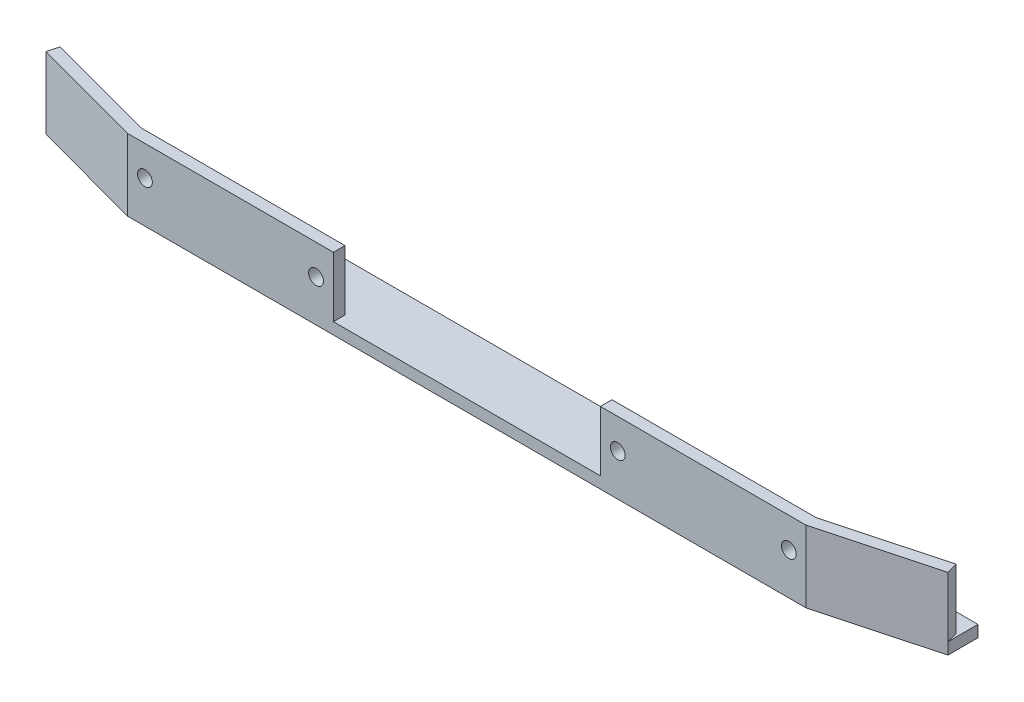
SolidWorks part; units mm, degrees
ref_plane "Front Plane" through (0, 0, 0) normal (0, 0, 1) x (1, 0, 0)
ref_plane "Top Plane" through (0, 0, 0) normal (0, 1, 0) x (1, 0, 0)
ref_plane "Right Plane" through (0, 0, 0) normal (1, 0, 0) x (0, 0, -1)
sketch "Sketch1" plane through (0, 0, 0) normal (0, 1, 0) x (1, 0, 0)
  line L0 (-58.6068, 6.5) -> (-34.4666, 0)
  line L1 (-58.6068, 13) -> (136.3932, 13)
  line L2 (-58.6068, 13) -> (-58.6068, 6.5)
  line L3 (-34.4666, 0) -> (112.253, 0)
  line L4 (136.3932, 13) -> (136.3932, 6.5)
  line L5 (136.3932, 6.5) -> (112.253, 0)
  circle A0 centre (-11.6068, 9.25) radius 1.5
  circle A1 centre (89.3932, 9.25) radius 1.5
  point P12 (0, 0)
  dimension "D7" = 9.25
  dimension "D8" = 3
  dimension "D2" = 195
  dimension "D3" = 25
  dimension "D4" = 25
  dimension "D5" = 13
  dimension "D10" = 2
extrude "Boss-Extrude1" add sketch "Sketch1" along normal blind 2.5
sketch "Sketch2" plane through (0, 2.5, 0) normal (0, 1, 0) x (1, 0, 0)
  line L0 (-58.6068, 6.5) -> (-34.4666, 0)
  line L1 (-34.4666, 0) -> (10.0334, 0)
  line L2 (-34.4666, 0) -> (112.253, 0) construction
  line L3 (10.0334, 0) -> (10.0334, 2.5)
  line L4 (10.0334, 2.5) -> (-34.1359, 2.5)
  line L5 (-34.1359, 2.5) -> (-57.9568, 8.914)
  line L6 (-57.9568, 8.914) -> (-58.6068, 6.5)
  line L7 (136.3932, 6.5) -> (112.253, 0)
  line L8 (112.253, 0) -> (67.753, 0)
  line L9 (67.753, 0) -> (67.753, 2.5)
  line L10 (67.753, 2.5) -> (111.9223, 2.5)
  line L11 (111.9223, 2.5) -> (135.7432, 8.914)
  line L12 (135.7432, 8.914) -> (136.3932, 6.5)
  dimension "D1" = 2.5
  dimension "D2" = 2.5
  dimension "D3" = 2.5
  dimension "D4" = 2.5
  dimension "D5" = 44.5
  dimension "D6" = 44.5
extrude "Boss-Extrude2" add sketch "Sketch2" along normal blind 13
sketch "Sketch3" plane through (0, 0, 0) normal (0, 0, 1) x (1, 0, 0)
  line L0 (-34.4666, 15.5) -> (10.0334, 15.5) construction
  line L2 (67.753, 15.5) -> (112.253, 15.5) construction
  circle A0 centre (-30.7166, 9) radius 1.6
  circle A1 centre (6.2834, 9) radius 1.6
  circle A2 centre (71.503, 9) radius 1.6
  circle A3 centre (108.503, 9) radius 1.6
  point P8 (0, 0)
  point P9 (0, 0)
  point P12 (-12.2166, 15.5)
  point P15 (90.003, 15.5)
  dimension "D1" = 3.2
  dimension "D2" = 6.5
  dimension "D3" = 37
  dimension "D4" = 37
  dimension "D5" = 18.5
  dimension "D6" = 18.5
extrude "Cut-Extrude1" cut sketch "Sketch3" against normal blind 13
